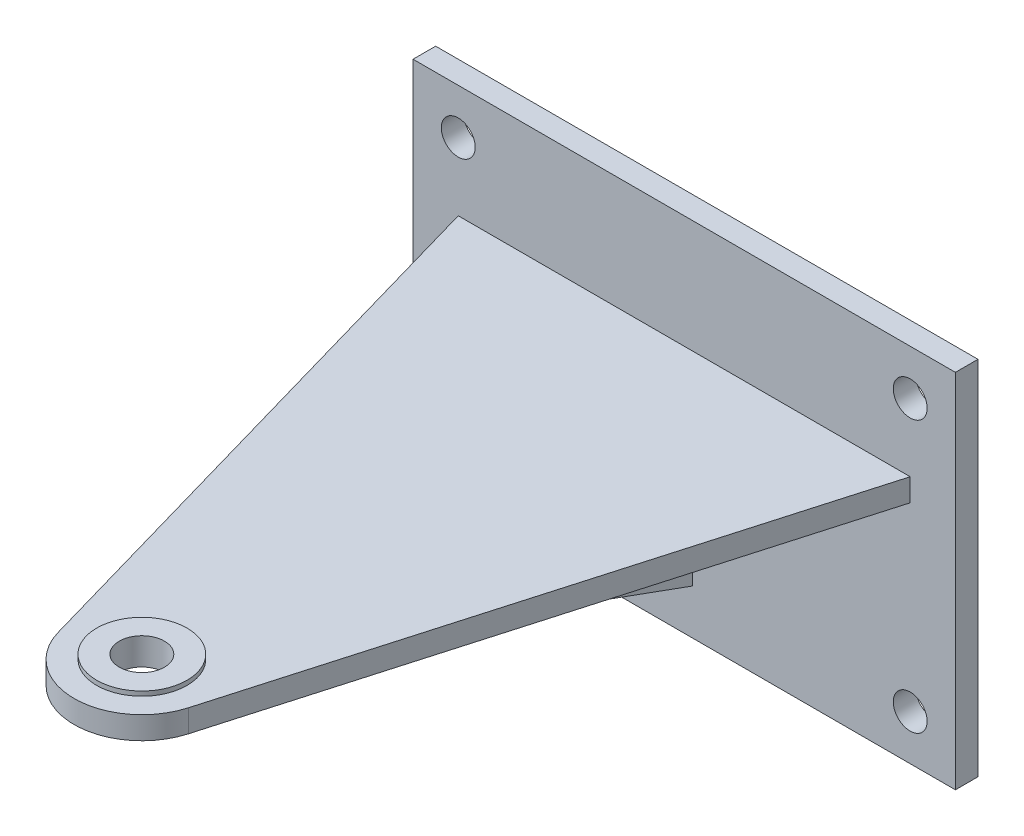
SolidWorks part; units mm, degrees
material "ABS"
ref_plane "Front Plane" through (0, 0, 0) normal (0, 0, 1) x (1, 0, 0)
ref_plane "Top Plane" through (0, 0, 0) normal (0, 1, 0) x (1, 0, 0)
ref_plane "Right Plane" through (0, 0, 0) normal (1, 0, 0) x (0, 0, -1)
sketch "Sketch1" plane through (0, 0, 0) normal (0, 0, 1) x (1, 0, 0)
  line L1 (76.2, -50.8) -> (-76.2, -50.8)
  line L2 (76.2, -50.8) -> (76.2, 50.8)
  line L3 (76.2, 50.8) -> (-76.2, 50.8)
  line L4 (-76.2, -50.8) -> (-76.2, 50.8)
  line L5 (76.2, -50.8) -> (-76.2, 50.8) construction
  line L6 (76.2, 50.8) -> (-76.2, -50.8) construction
  point P0 (0, 0)
  dimension "D1" = 152.4
  dimension "D2" = 101.6
extrude "Boss-Extrude1" add sketch "Sketch1" along normal blind 6.35
ref_plane "Plane1" through (0, 19.05, 0) normal (0, 1, 0) x (1, 0, 0)
sketch "Sketch4" plane through (0, 19.05, 0) normal (0, 1, 0) x (1, 0, 0)
  line L0 (0, 0) -> (0, -80.788) construction
  line L1 (63.5, -6.35) -> (18.3126, -163.999)
  line L2 (76.2, -6.35) -> (-76.2, -6.35) construction
  line L3 (-63.5, -6.35) -> (-18.3126, -163.999)
  line L4 (-63.5, -6.35) -> (63.5, -6.35)
  arc A0 (18.3126, -163.999) -> (-18.3126, -163.999) centre (0, -158.75) cw
  point P10 (0, -6.35)
  dimension "D2" = 19.05
  dimension "D1" = 127
  dimension "D3" = 152.4
extrude "Boss-Extrude2" add sketch "Sketch4" against normal blind 6.35
sketch "Sketch5" plane through (0, 19.05, 0) normal (0, 1, 0) x (1, 0, 0)
  circle A0 centre (0, -158.75) radius 12.7
  dimension "D1" = 25.4
extrude "Boss-Extrude3" add sketch "Sketch5" along normal blind 1.27
sketch "Sketch6" plane through (0, 0, 0) normal (1, 0, 0) x (0, 0, -1)
  line L0 (-6.35, -38.1) -> (-146.05, 12.7)
  line L1 (-6.35, -50.8) -> (-6.35, 50.8) construction
  line L2 (-163.999, 12.7) -> (-6.35, 12.7) construction
  line L3 (-6.35, 12.7) -> (-146.05, 12.7)
  line L4 (-6.35, 12.7) -> (-6.35, -38.1)
  dimension "D1" = 139.7
  dimension "D2" = 50.8
extrude "Boss-Extrude4" add sketch "Sketch6" along normal mid plane 4.7625
ref_plane "Plane2" through (25.4, 0, 0) normal (1, 0, 0) x (0, 0, -1)
sketch "Sketch7" plane through (25.4, 0, 0) normal (1, 0, 0) x (0, 0, -1)
  line L0 (-57.15, 12.7) -> (-6.35, -12.7)
  line L1 (-6.35, 12.7) -> (-146.05, 12.7) construction
  line L2 (-6.35, -50.8) -> (-6.35, 50.8) construction
  dimension "D1" = 50.8
  dimension "D2" = 25.4
rib "Rib1" sketch "Sketch7" sketch "Sketch7" thickness 2.54 extrusion direction parallel to sketch draft on no parameters "D1"=2.54
mirror "Mirror1" about plane through (0, 0, 0) normal (1, 0, 0) of "Rib1"
sketch "Sketch8" plane through (0, 20.32, 0) normal (0, 1, 0) x (1, 0, 0)
  circle A0 centre (0, -158.75) radius 6.35
  dimension "D1" = 12.7
extrude "Cut-Extrude1" cut sketch "Sketch8" against normal through all
sketch "Sketch9" plane through (0, 0, 6.35) normal (0, 0, 1) x (1, 0, 0)
  line L0 (-76.2, 50.8) -> (-76.2, -50.8) construction
  line L1 (76.2, 50.8) -> (-76.2, 50.8) construction
  circle A0 centre (-63.5, 38.1) radius 4.7625
  point P4 (0, 0)
  dimension "D1" = 9.525
  dimension "D2" = 12.7
  dimension "D3" = 12.7
extrude "Cut-Extrude2" cut sketch "Sketch9" against normal through all both and the other way through all
pattern_linear "LPattern1" count 2 spacing 127 along (1, 0, 0) count 2 spacing 76.2 along (0, -1, 0) of "Cut-Extrude2"
